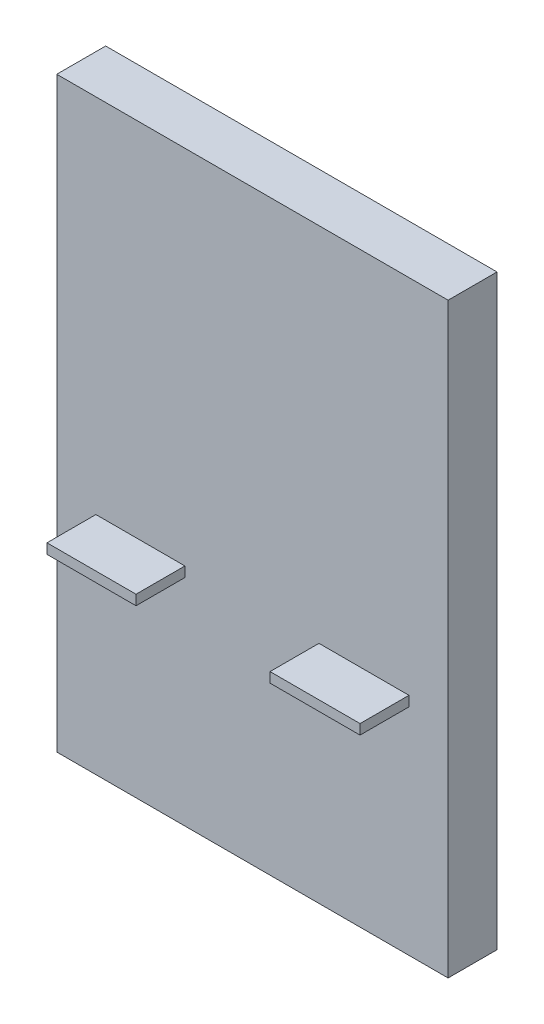
SolidWorks part; units mm, degrees
ref_plane "Front Plane" through (0, 0, 0) normal (0, 0, 1) x (1, 0, 0)
ref_plane "Top Plane" through (0, 0, 0) normal (0, 1, 0) x (1, 0, 0)
ref_plane "Right Plane" through (0, 0, 0) normal (1, 0, 0) x (0, 0, -1)
sketch "Sketch1" plane through (0, 0, 0) normal (0, 0, 1) x (1, 0, 0)
  line L1 (-1, 0) -> (1, 0)
  line L2 (-1, 0) -> (-1, 3)
  line L3 (-1, 3) -> (1, 3)
  line L4 (1, 0) -> (1, 3)
  point P6 (-1.8768, 1.1437)
  dimension "D1" = 2
  dimension "D2" = 1
  dimension "D3" = 1
  dimension "D4" = 3
extrude "Boss-Extrude1" add sketch "Sketch1" against normal blind 0.25
sketch "Sketch2" plane through (0, 0, 0) normal (0, 0, 1) x (1, 0, 0)
  line L0 (-1, 0) -> (1, 0) construction
  line L1 (-0.8, 1.1) -> (-0.345, 1.1)
  line L2 (-0.8, 1.1) -> (-0.8, 1.1512)
  line L3 (-0.8, 1.1512) -> (-0.345, 1.1512)
  line L4 (-0.345, 1.1) -> (-0.345, 1.1512)
  line L5 (-1, 3) -> (-1, 0) construction
  line L6 (1, 0) -> (1, 3) construction
  line L7 (0.34, 1.1512) -> (0.8, 1.1512)
  line L8 (0.34, 1.1512) -> (0.34, 1.1)
  line L9 (0.34, 1.1) -> (0.8, 1.1)
  line L10 (0.8, 1.1512) -> (0.8, 1.1)
  point P4 (-0.5725, 1.1)
  dimension "D1" = 1.1
  dimension "D2" = 0.0512
  dimension "D3" = 0.2
  dimension "D4" = 0.2
  dimension "D5" = 0.0512
  dimension "D6" = 0.46
  dimension "D7" = 1.1
  dimension "D8" = 0.685
extrude "Boss-Extrude2" add sketch "Sketch2" along normal blind 0.25
